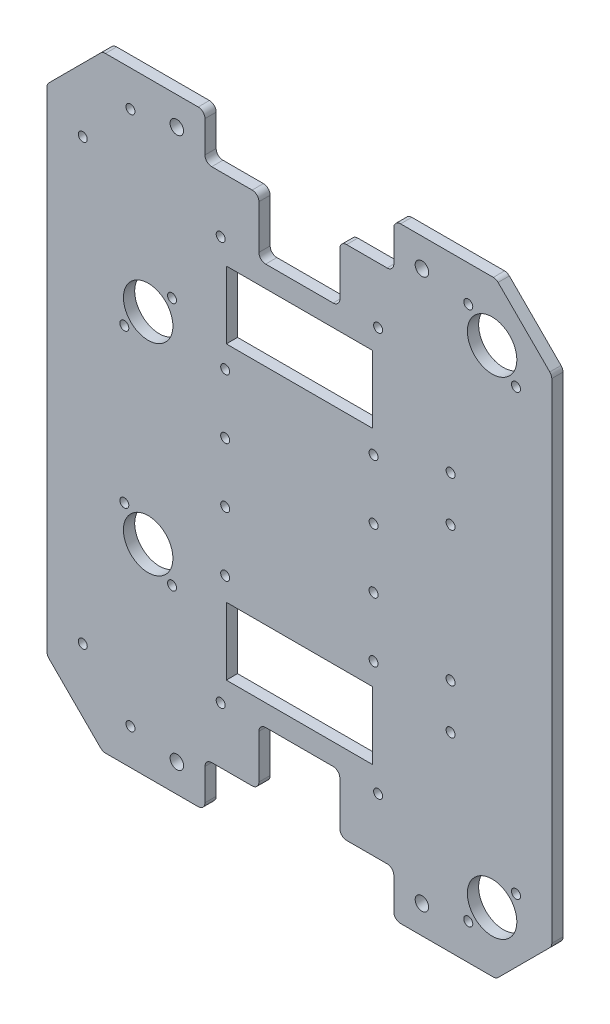
SolidWorks part; units mm, degrees
material "Alliage 1060"
ref_plane "Plan de dessus" through (0, 0, 0) normal (0, 0, 1) x (1, 0, 0)
ref_plane "Plan de droite" through (0, 0, 0) normal (0, 1, 0) x (1, 0, 0)
ref_plane "Plan de face" through (0, 0, 0) normal (1, 0, 0) x (0, 0, -1)
sketch "Esquisse1" plane through (0, 0, 0) normal (0, 0, 1) x (1, 0, 0)
  line L0 (0, 0) -> (-175, 0)
  line L1 (-175, 0) -> (-199.7487, 24.7487)
  line L2 (-199.7487, 24.7487) -> (-199.7487, 244.7487)
  line L3 (-199.7487, 244.7487) -> (-175, 269.4975)
  line L4 (-175, 269.4975) -> (0, 269.4975)
  line L5 (0, 269.4975) -> (24.7487, 244.7487)
  line L6 (24.7487, 244.7487) -> (24.7487, 24.7487)
  line L7 (24.7487, 24.7487) -> (0, 0)
  dimension "D1" = 220
  dimension "D2" = 35
  dimension "D3" = 135
  dimension "D4" = 175
extrude "Base" add sketch "Esquisse1" along normal blind 5
sketch "Esquisse3" plane through (0, 0, 0) normal (0, 0, -1) x (-1, 0, 0)
  line L0 (129.5, 0) -> (129.5, 20)
  line L1 (175, 0) -> (0, 0) construction
  line L2 (129.5, 20) -> (105.5, 20)
  line L3 (105.5, 20) -> (105.5, 45.5)
  line L4 (105.5, 45.5) -> (69.5, 45.5)
  line L5 (69.5, 45.5) -> (69.5, 20)
  line L6 (69.5, 20) -> (45.5, 20)
  line L7 (45.5, 20) -> (45.5, 0)
  line L8 (-24.7487, 134.7487) -> (199.7487, 134.7487) construction
  line L9 (-24.7487, 24.7487) -> (-24.7487, 244.7487) construction
  line L10 (199.7487, 244.7487) -> (199.7487, 24.7487) construction
  line L11 (45.5, 0) -> (129.5, 0)
  line L12 (45.5, 269.4975) -> (129.5, 269.4975)
  line L13 (129.5, 269.4975) -> (129.5, 249.4975)
  line L14 (129.5, 249.4975) -> (105.5, 249.4975)
  line L15 (105.5, 249.4975) -> (105.5, 223.9975)
  line L16 (105.5, 223.9975) -> (69.5, 223.9975)
  line L17 (69.5, 223.9975) -> (69.5, 249.4975)
  line L18 (69.5, 249.4975) -> (45.5, 249.4975)
  line L19 (45.5, 249.4975) -> (45.5, 269.4975)
  line L20 (87.5, 45.5) -> (87.5, -49954.5) construction
  line L21 (0, 269.4975) -> (175, 269.4975) construction
  line L22 (55, 214.4975) -> (120, 214.4975)
  line L23 (55, 214.4975) -> (55, 184.4975)
  line L24 (55, 184.4975) -> (120, 184.4975)
  line L25 (120, 214.4975) -> (120, 184.4975)
  line L26 (120, 55) -> (120, 85)
  line L27 (55, 85) -> (120, 85)
  line L28 (55, 55) -> (120, 55)
  line L29 (55, 55) -> (55, 85)
  circle A0 centre (52.5, 45) radius 2
  circle A1 centre (122.5, 45) radius 2
  circle A2 centre (122.5, 224.4975) radius 2
  circle A3 centre (52.5, 224.4975) radius 2
  point P4 (87.5, 45.5)
  point P11 (87.5, 0)
  point P40 (87.5, 214.4975)
  dimension "D7" = 4
  dimension "D5" = 25
  dimension "D1" = 20
  dimension "D2" = 24
  dimension "D3" = 36
  dimension "D4" = 25.5
  dimension "D6" = 7
  dimension "D8" = 55
  dimension "D9" = 30
  dimension "D10" = 65
extrude "Enlèv. mat.-Extru.1" cut sketch "Esquisse3" against normal through all
fillet "Congé1" radius 3 24 edges at (-199.7487, 24.7487, 2.5) (24.7487, 24.7487, 2.5) (0, 0, 2.5) (-129.5, 20, 2.5) (-105.5, 45.5, 2.5) (-105.5, 20, 2.5) (-175, 0, 2.5) (-129.5, 0, 2.5) (-69.5, 45.5, 2.5) (-45.5, 20, 2.5) (-69.5, 20, 2.5) (-45.5, 0, 2.5) (24.7487, 244.7487, 2.5) (-129.5, 249.4975, 2.5) (-105.5, 223.9975, 2.5) (-199.7487, 244.7487, 2.5) (-175, 269.4975, 2.5) (-129.5, 269.4975, 2.5) (-105.5, 249.4975, 2.5) (-69.5, 223.9975, 2.5) (-45.5, 249.4975, 2.5) (-69.5, 249.4975, 2.5) (-45.5, 269.4975, 2.5) (0, 269.4975, 2.5)
sketch "Esquisse6" plane through (0, 0, 5) normal (0, 0, 1) x (1, 0, 0)
  line L0 (-144.1421, 190.1041) -> (-165.3553, 168.8909) construction
  line L1 (0.8787, 0.8787) -> (23.8701, 23.8701) construction
  line L2 (-87.5, 231.5685) -> (-87.5, -49768.4315) construction
  line L3 (-132.5, 269.4975) -> (-173.7574, 269.4975) construction
  line L4 (-55, 184.4975) -> (-120, 184.4975) construction
  line L5 (-203.2843, 134.7487) -> (49796.7157, 134.7487) construction
  line L6 (-199.7487, 243.5061) -> (-199.7487, 25.9914) construction
  line L7 (-12.3909, 253.6041) -> (8.8223, 232.3909) construction
  line L8 (8.8223, 37.1066) -> (-12.3909, 15.8934) construction
  line L9 (-42.5, 0) -> (-1.2426, 0) construction
  line L10 (-175.8787, 268.6188) -> (-198.8701, 245.6274) construction
  line L11 (-144.1421, 79.3934) -> (-165.3553, 100.6066) construction
  line L12 (-183.8388, 37.1231) -> (-162.6256, 15.9099) construction
  line L13 (-187.3744, 12.3744) -> (-165.2409, 34.5079) construction
  line L14 (-198.8701, 23.8701) -> (-175.8787, 0.8787) construction
  line L15 (-187.3744, 257.1231) -> (-165.2409, 234.9896) construction
  line L16 (-183.8388, 232.3744) -> (-162.6256, 253.5876) construction
  circle A2 centre (-12.3909, 15.8934) radius 2
  circle A3 centre (8.8223, 37.1066) radius 2
  circle A4 centre (8.8223, 232.3909) radius 2
  circle A5 centre (-12.3909, 253.6041) radius 2
  circle A10 centre (-1.7843, 242.9975) radius 11
  circle A11 centre (-1.7843, 26.5) radius 11
  circle A16 centre (-144.1421, 190.1041) radius 2
  circle A17 centre (-165.3553, 168.8909) radius 2
  circle A21 centre (-154.7487, 179.4975) radius 11
  circle A22 centre (-165.3553, 100.6066) radius 2
  circle A23 centre (-154.7487, 90) radius 11
  circle A24 centre (-144.1421, 79.3934) radius 2
  circle A25 centre (-183.8388, 37.1231) radius 2
  circle A26 centre (-162.6256, 15.9099) radius 2
  circle A27 centre (-162.6256, 253.5876) radius 2
  circle A28 centre (-183.8388, 232.3744) radius 2
  point P15 (-87.5, 184.4975)
  point P20 (-199.7487, 134.7487)
  point P44 (-173.2322, 26.5165)
  point P54 (-187.3744, 12.3744)
  dimension "D2" = 20
  dimension "D3" = 22
  dimension "D4" = 30
  dimension "D5" = 26.5
  dimension "D7" = 4
  dimension "D8" = 22
  dimension "D9" = 22
  dimension "D10" = 30
  dimension "D1" = 4
  dimension "D6" = 4
  dimension "D11" = 45
  dimension "D12" = 90
  dimension "D13" = 4
  dimension "D14" = 4
  dimension "D15" = 30
  dimension "D16" = 20
extrude "Perçage pour billes" cut sketch "Esquisse6" against normal up to next
sketch "Esquisse8" plane through (0, 0, 5) normal (0, 0, 1) x (1, 0, 0)
  line L0 (-87.5, 223.9975) -> (-87.5, 85) construction
  line L1 (-72.5, 223.9975) -> (-102.5, 223.9975) construction
  line L2 (-120, 85) -> (-55, 85) construction
  line L3 (-132.5, 269.4975) -> (-173.7574, 269.4975) construction
  line L4 (-129.5, 252.4975) -> (-129.5, 266.4975) construction
  line L5 (-173.7574, 0) -> (-132.5, 0) construction
  line L6 (-129.5, 3) -> (-129.5, 17) construction
  circle A0 centre (-142, 12.5) radius 3
  circle A1 centre (-142, 256.9975) radius 3
  circle A2 centre (-33, 256.9975) radius 3
  circle A3 centre (-33, 12.5) radius 3
  dimension "D1" = 12.5
  dimension "D2" = 12.5
  dimension "D3" = 6
  dimension "D4" = 12.5
  dimension "D5" = 12.5
  dimension "D6" = 6
extrude "Perçage pour profilé" cut sketch "Esquisse8" against normal up to next
sketch "Esquisse10" plane through (0, 0, 5) normal (0, 0, 1) x (1, 0, 0)
  line L0 (-199.7487, 243.5061) -> (-199.7487, 25.9914) construction
  line L2 (-55, 184.4975) -> (-120, 184.4975) construction
  line L3 (-87.5, 184.4975) -> (-87.5, 85) construction
  line L4 (-120, 85) -> (-55, 85) construction
  line L5 (-199.7487, 134.7487) -> (24.7487, 134.7487) construction
  line L6 (24.7487, 25.9914) -> (24.7487, 243.5061) construction
  circle A0 centre (-120.5, 174.4975) radius 2
  circle A1 centre (-120.5, 147.9975) radius 2
  circle A2 centre (-54.5, 147.9975) radius 2
  circle A3 centre (-54.5, 174.4975) radius 2
  circle A4 centre (-54.5, 121.5) radius 2
  circle A5 centre (-54.5, 95) radius 2
  circle A6 centre (-120.5, 121.5) radius 2
  circle A7 centre (-120.5, 95) radius 2
  dimension "D1" = 26.5
  dimension "D2" = 33
  dimension "D3" = 4
  dimension "D4" = 4
  dimension "D5" = 10
extrude "Enlèv. mat.-Extru.3" cut sketch "Esquisse10" against normal through all
sketch "Esquisse13" plane through (0, 0, 5) normal (0, 0, 1) x (1, 0, 0)
  line L0 (24.7487, 134.7487) -> (-199.7487, 134.7487) construction
  line L1 (24.7487, 25.9914) -> (24.7487, 243.5061) construction
  line L2 (-199.7487, 243.5061) -> (-199.7487, 25.9914) construction
  circle A0 centre (-20.2513, 184.7487) radius 2
  circle A1 centre (-20.2513, 164.7487) radius 2
  circle A2 centre (-20.2513, 104.7487) radius 2
  circle A3 centre (-20.2513, 84.7487) radius 2
  dimension "D1" = 4
  dimension "D2" = 4
  dimension "D3" = 20
  dimension "D4" = 30
  dimension "D5" = 45
extrude "Enlèv. mat.-Extru.4" cut sketch "Esquisse13" against normal blind 10
